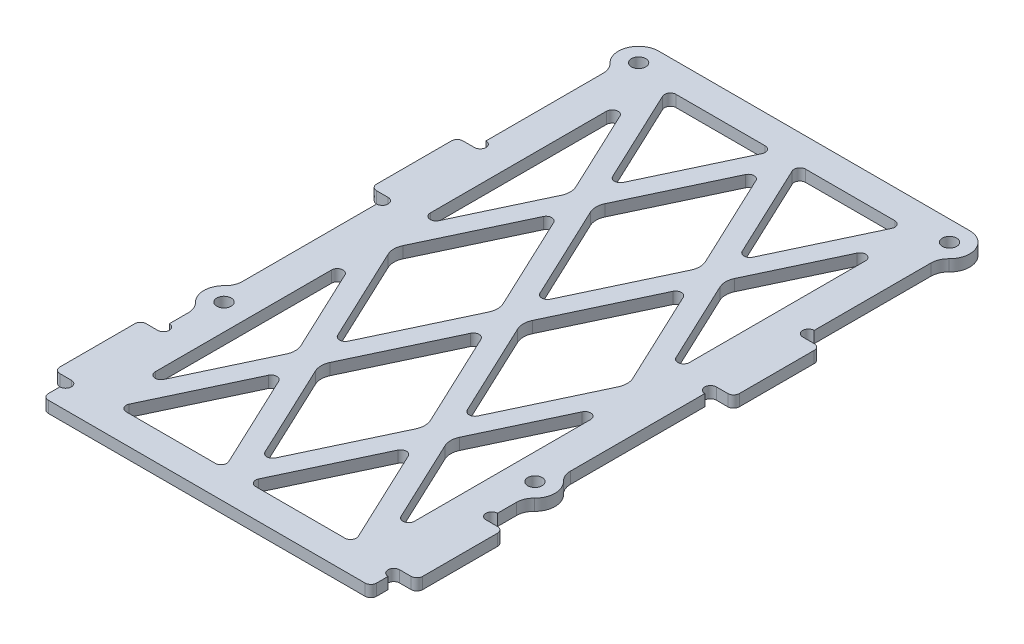
SolidWorks part; units mm, degrees
material "Thornel Mat VMA"
ref_plane "前视基准面" through (0, 0, 0) normal (0, 0, 1) x (1, 0, 0)
ref_plane "上视基准面" through (0, 0, 0) normal (0, 1, 0) x (1, 0, 0)
ref_plane "右视基准面" through (0, 0, 0) normal (1, 0, 0) x (0, 0, -1)
sketch "草图1" plane through (0, 0, 0) normal (0, 1, 0) x (1, 0, 0)
  line L0 (-28.5, 31.3096) -> (-28.5, 9)
  line L5 (0, 39.5) -> (0, -39.5) construction
  line L6 (23.9594, 0) -> (-23.9594, 0) construction
  line L7 (27, 39.5) -> (-27, 39.5)
  line L8 (28.5, 31.3096) -> (28.5, 9)
  line L10 (-28.5, -40.6904) -> (-28.5, -46)
  line L12 (-28.5, -61) -> (-28.5, -66)
  line L13 (-28.5, -46) -> (-31.5, -46)
  line L15 (-28.5, -61) -> (-31.5, -61)
  line L16 (-31.5, -46) -> (-31.5, -61)
  line L22 (31.5, -46) -> (31.5, -61)
  line L23 (28.5, -61) -> (31.5, -61)
  line L24 (28.5, -61) -> (28.5, -66)
  line L28 (28.5, -46) -> (31.5, -46)
  line L29 (28.5, -40.6904) -> (28.5, -46)
  line L49 (-28.5, -66) -> (28.5, -66)
  line L53 (0, -1.1) -> (0, 1.1) construction
  line L54 (-28.5, -31.3096) -> (-28.5, -6)
  line L55 (31.5, 9) -> (31.5, -6)
  line L56 (-28.5, 9) -> (-31.5, 9)
  line L58 (-28.5, -6) -> (-31.5, -6)
  line L59 (-31.5, 9) -> (-31.5, -6)
  line L60 (28.5, -6) -> (31.5, -6)
  line L61 (28.5, 9) -> (31.5, 9)
  line L62 (28.5, -6) -> (28.5, -31.3096)
  circle A0 centre (-27, 36) radius 1.25
  arc A1 (-27, 39.5) -> (-29.4231, 33.4744) centre (-27, 36) ccw
  arc A3 (-29.4231, 33.4744) -> (-28.5, 31.3096) centre (-31.5, 31.3096) cw
  arc A4 (29.4231, 33.4744) -> (28.5, 31.3096) centre (31.5, 31.3096) ccw
  arc A5 (27, 39.5) -> (29.4231, 33.4744) centre (27, 36) cw
  arc A6 (29.4231, -38.5256) -> (29.4231, -33.4744) centre (27, -36) ccw
  arc A7 (29.4231, -33.4744) -> (28.5, -31.3096) centre (31.5, -31.3096) cw
  arc A8 (-29.4231, -33.4744) -> (-28.5, -31.3096) centre (-31.5, -31.3096) ccw
  arc A9 (-29.4231, -38.5256) -> (-29.4231, -33.4744) centre (-27, -36) cw
  circle A10 centre (-27, -36) radius 1.25
  circle A11 centre (27, 36) radius 1.25
  circle A12 centre (27, -36) radius 1.25
  arc A13 (-29.4231, -38.5256) -> (-28.5, -40.6904) centre (-31.5, -40.6904) cw
  arc A14 (29.4231, -38.5256) -> (28.5, -40.6904) centre (31.5, -40.6904) ccw
  dimension "D1" = 72
  dimension "D3" = 2.5
  dimension "D4" = 57
  dimension "D5" = 3.5
  dimension "D6" = 3
  dimension "D7" = 3
  dimension "D2" = 54
  dimension "D8" = 15
  dimension "D10" = 5
  dimension "D13" = 10
  dimension "D15" = 40
  dimension "D16" = 15
extrude "凸台-拉伸1" add sketch "草图1" along normal blind 2
sketch "草图2" plane through (0, 2, 0) normal (0, 1, 0) x (1, 0, 0)
  line L0 (-28.5, 31.3096) -> (-28.5, 9) construction
  line L1 (-28.5, -40.6904) -> (-28.5, -46) construction
  line L2 (-28.5, -61) -> (-28.5, -66) construction
  line L3 (-28.5, -6) -> (-28.5, -31.3096) construction
  line L8 (0, -1.1) -> (0, 1.1) construction
  line L9 (27, 39.5) -> (-27, 39.5) construction
  line L10 (-22.5, 34.5) -> (22.5, 34.5)
  line L11 (-22.5, 34.5) -> (-22.5, -61)
  line L12 (-22.5, -61) -> (22.5, -61)
  line L13 (22.5, 34.5) -> (22.5, -61)
  line L15 (-28.5, -66) -> (28.5, -66) construction
  line L17 (-28.5, 31.3096) -> (-28.5, 9) construction
  line L18 (28.5, 9) -> (28.5, 31.3096) construction
  circle A2 centre (-28.5, -45) radius 1
  circle A3 centre (-28.5, -62) radius 1
  circle A20 centre (28.5, -62) radius 1
  circle A21 centre (28.5, -45) radius 1
  circle A22 centre (-28.5, 10) radius 1
  circle A23 centre (-28.5, -7) radius 1
  circle A24 centre (28.5, -7) radius 1
  circle A25 centre (28.5, 10) radius 1
  dimension "D1" = 2
  dimension "D2" = 6
  dimension "D3" = 5
  dimension "D4" = 6
  dimension "D5" = 5
extrude "切除-拉伸1" cut sketch "草图2" against normal through all
sketch "草图3" plane through (0, 2, 0) normal (0, 1, 0) x (1, 0, 0)
  line L0 (-22.5, 34.5) -> (22.5, -61)
  line L1 (-22.5, -61) -> (22.5, 34.5)
  line L2 (0, 34.5) -> (-22.5, -13.25)
  line L3 (22.5, 34.5) -> (-22.5, 34.5) construction
  line L4 (-22.5, 34.5) -> (-22.5, -61) construction
  line L5 (-22.5, -13.25) -> (0, -61)
  line L6 (-22.5, -61) -> (22.5, -61) construction
  line L7 (0, -61) -> (22.5, -13.25)
  line L8 (22.5, -61) -> (22.5, 34.5) construction
  line L9 (22.5, -13.25) -> (0, 34.5)
extrude "拉伸-薄壁1" add sketch "草图3" against normal up to surface (2 mm away) thin up to face at (0, 0, 20.8402) thin type mid plane wall 3.5
fillet "圆角1" radius 1 10 edges at (-31.5, 1, 61) (-31.5, 1, 46) (31.5, 1, 61) (31.5, 1, 46) (28.5, 1, 66) (-28.5, 1, 66) (31.5, 1, 6) (31.5, 1, -9) (-31.5, 1, 6) (-31.5, 1, -9)
fillet "圆角2" radius 1 28 edges at (11.25, 1, -6.5195) (11.25, 1, 33.0195) (0, 1, -30.3945) (0, 1, 9.1445) (0, 1, 56.8945) (0, 1, 17.3555) (-11.25, 1, 33.0195) (-11.25, 1, -6.5195) (-22.5, 1, 17.3555) (-22.5, 1, 56.8945) (-1.9345, 1, -34.5) (-11.25, 1, -14.7305) (-20.5655, 1, -34.5) (-11.25, 1, 41.2305) (-1.9345, 1, 61) (-20.5655, 1, 61) (11.25, 1, -14.7305) (1.9345, 1, -34.5) (20.5655, 1, -34.5) (22.5, 1, 9.1445) (22.5, 1, -30.3945) (22.5, 1, 17.3555) (22.5, 1, 56.8945) (-22.5, 1, 9.1445) (1.9345, 1, 61) (11.25, 1, 41.2305) (20.5655, 1, 61) (-22.5, 1, -30.3945)
fillet "圆角3" radius 3 12 edges at (13.1845, 1, 37.125) (9.3155, 1, 37.125) (-9.3155, 1, 37.125) (-13.1845, 1, 37.125) (-1.9345, 1, 13.25) (1.9345, 1, 13.25) (13.1845, 1, -10.625) (9.3155, 1, -10.625) (-9.3155, 1, -10.625) (-13.1845, 1, -10.625) (20.5655, 1, 13.25) (-20.5655, 1, 13.25)
